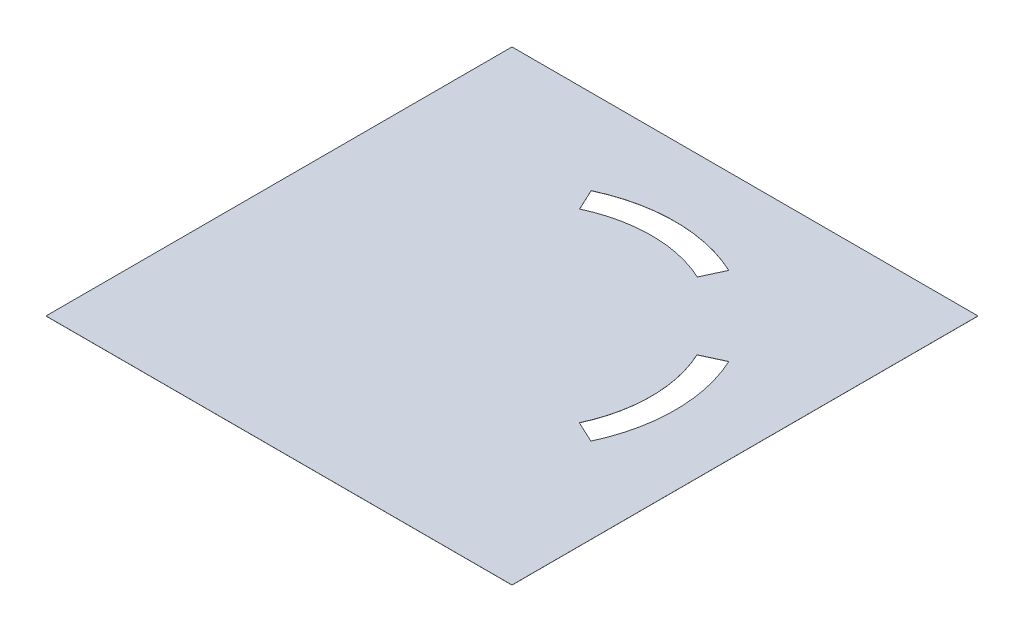
SolidWorks part; units mm, degrees
ref_plane "Front Plane" through (0, 0, 0) normal (0, 0, 1) x (1, 0, 0)
ref_plane "Top Plane" through (0, 0, 0) normal (0, 1, 0) x (1, 0, 0)
ref_plane "Right Plane" through (0, 0, 0) normal (1, 0, 0) x (0, 0, -1)
sketch "Sketch1" plane through (0, 0, 0) normal (0, 1, 0) x (1, 0, 0)
  line L0 (0, 0) -> (0, 107.07)
  line L1 (0, 0) -> (107.07, 0)
  line L2 (0, 107.07) -> (107.07, 107.07)
  line L3 (107.07, 107.07) -> (107.07, 0)
  line L10 (40.021, 82.5764) -> (37.6953, 87.5639)
  line L13 (67.0772, 82.5764) -> (69.3747, 87.5034)
  line L14 (82.5187, 67.0503) -> (87.5034, 69.3747)
  line L15 (82.5187, 40.0197) -> (87.5034, 37.6953)
  arc A0 (37.6953, 87.5639) -> (69.3747, 87.5034) centre (53.4708, 53.8846) cw
  arc A1 (40.021, 82.5764) -> (67.0772, 82.5764) centre (53.5491, 53.5652) cw
  arc A2 (82.5187, 67.0503) -> (82.5187, 40.0197) centre (53.535, 53.535) cw
  arc A3 (87.5034, 69.3747) -> (87.5034, 37.6953) centre (53.535, 53.535) cw
extrude "Boss-Extrude1" add sketch "Sketch1" along normal blind 0.02
scale "Scale2" scale about centroid uniform scaling yes scale factor 0.75
